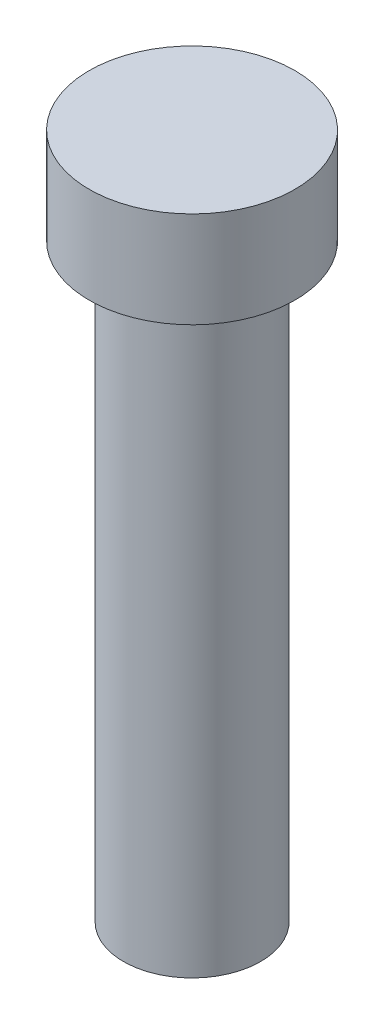
SolidWorks part; units mm, degrees
ref_plane "Front Plane" through (0, 0, 0) normal (0, 0, 1) x (1, 0, 0)
ref_plane "Top Plane" through (0, 0, 0) normal (0, 1, 0) x (1, 0, 0)
ref_plane "Right Plane" through (0, 0, 0) normal (1, 0, 0) x (0, 0, -1)
sketch "Sketch1" plane through (0, 0, 0) normal (0, 0, 1) x (1, 0, 0)
  line L0 (7.5, 50) -> (7.5, 43)
  line L1 (0, 0) -> (5, 0)
  line L2 (0, 0) -> (0, 50)
  line L3 (0, 50) -> (7.5, 50)
  line L5 (7.5, 43) -> (5, 43)
  line L6 (5, 43) -> (5, 0)
  dimension "D1" = 50
  dimension "D2" = 7.5
  dimension "D3" = 5
  dimension "D4" = 7
revolve "Revolve1" add sketch "Sketch1" angle 360 about L2
